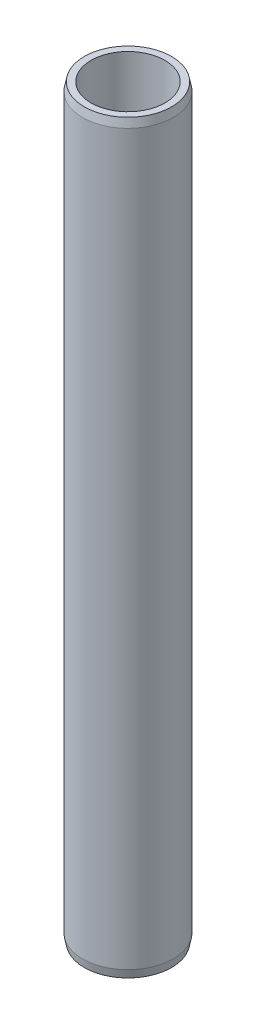
SolidWorks part; units mm, degrees
ref_plane "Plan de face" through (0, 0, 0) normal (0, 0, 1) x (1, 0, 0)
ref_plane "Plan de dessus" through (0, 0, 0) normal (0, 1, 0) x (1, 0, 0)
ref_plane "Plan de droite" through (0, 0, 0) normal (1, 0, 0) x (0, 0, -1)
sketch "Esquisse1" plane through (0, 0, 0) normal (0, 1, 0) x (1, 0, 0)
  circle A0 centre (0, 0) radius 11
  circle A1 centre (0, 0) radius 13.5
  dimension "D1" = 27
  dimension "D2" = 22
extrude "Extrusion1" add sketch "Esquisse1" along normal mid plane 222
chamfer "Chanfrein1" distance 0.5 distance2 2.5 1 edges at (0, -111, 13.5)
chamfer "Chanfrein2" distance 2.5 distance2 0.5 1 edges at (0, 111, 13.5)
